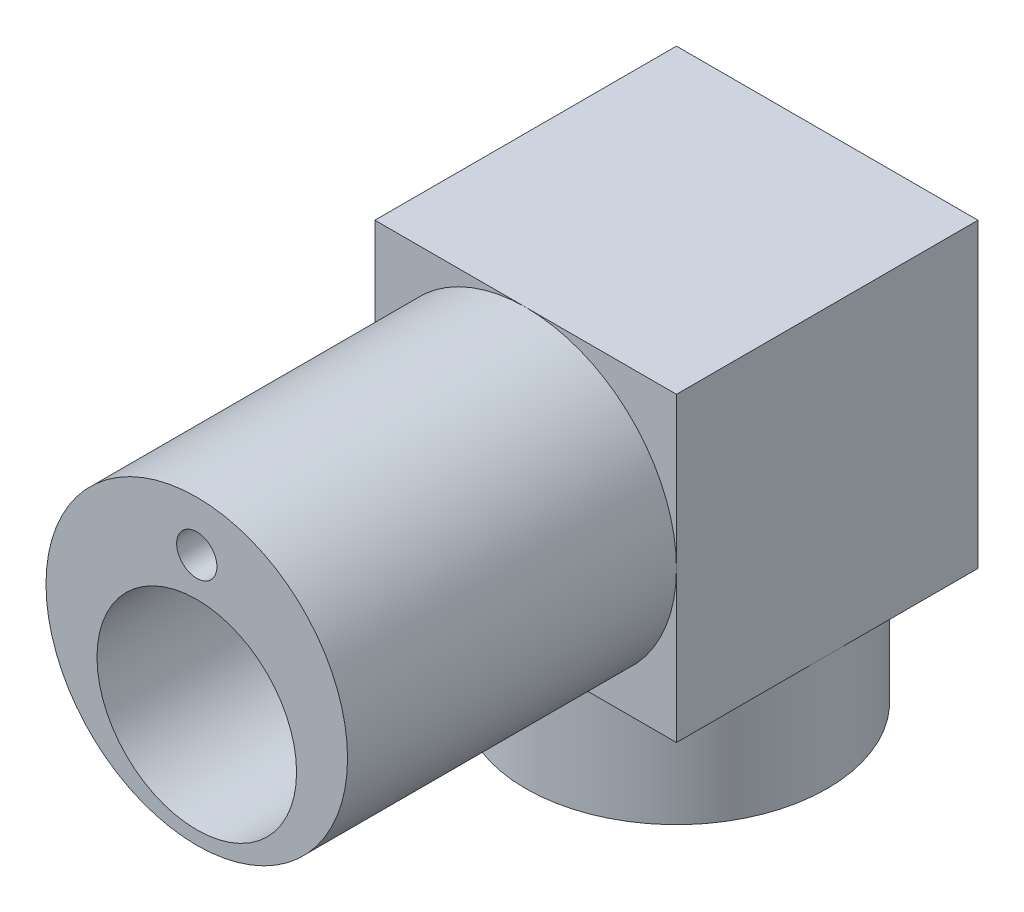
SolidWorks part; units mm, degrees
ref_plane "Front Plane" through (0, 0, 0) normal (0, 0, 1) x (1, 0, 0)
ref_plane "Top Plane" through (0, 0, 0) normal (0, 1, 0) x (1, 0, 0)
ref_plane "Right Plane" through (0, 0, 0) normal (1, 0, 0) x (0, 0, -1)
sketch "Sketch1" plane through (0, 0, 0) normal (0, 0, 1) x (1, 0, 0)
  circle A0 centre (0, 0) radius 28.1
extrude "Boss-Extrude2" add sketch "Sketch1" along normal blind 61.3
sketch "Sketch3" plane through (0, 0, 61.3) normal (0, 0, 1) x (1, 0, 0)
  circle A1 centre (0, -7) radius 18.6
extrude "Cut-Extrude2" cut sketch "Sketch3" against normal blind 58.8 contours A1
sketch "Sketch4" plane through (0, 0, 0) normal (0, 0, -1) x (-1, 0, 0)
  line L1 (-28.1, -28.1) -> (28.1, -28.1)
  line L2 (-28.1, -28.1) -> (-28.1, 28.1)
  line L3 (-28.1, 28.1) -> (28.1, 28.1)
  line L4 (28.1, -28.1) -> (28.1, 28.1)
  line L5 (-28.1, -28.1) -> (28.1, 28.1) construction
  line L6 (-28.1, 28.1) -> (28.1, -28.1) construction
  point P0 (0, 0)
extrude "Boss-Extrude3" add sketch "Sketch4" along normal blind 56.2
sketch "Sketch5" plane through (0, 0, 2.5) normal (0, 0, 1) x (1, 0, 0)
  circle A1 centre (0, -7) radius 16.1
extrude "Cut-Extrude4" cut sketch "Sketch5" against normal blind 5
sketch "Sketch6" plane through (0, 0, -56.2) normal (0, 0, -1) x (-1, 0, 0)
  line L1 (-24.8987, -24.8896) -> (24.8987, -24.8896)
  line L2 (-24.8987, -24.8896) -> (-24.8987, 24.8896)
  line L3 (-24.8987, 24.8896) -> (24.8987, 24.8896)
  line L4 (24.8987, -24.8896) -> (24.8987, 24.8896)
  line L5 (-24.8987, -24.8896) -> (24.8987, 24.8896) construction
  line L6 (-24.8987, 24.8896) -> (24.8987, -24.8896) construction
  point P0 (0, 0)
extrude "Cut-Extrude5" cut sketch "Sketch6" against normal blind 53.7
sketch "Sketch7" plane through (0, -28.1, 0) normal (0, -1, 0) x (-1, 0, 0)
  circle A0 centre (0, 28.1) radius 28.1
extrude "Boss-Extrude4" add sketch "Sketch7" along normal blind 21.5 contours A0
sketch "Sketch8" plane through (0, -49.6, 0) normal (0, -1, 0) x (-1, 0, 0)
  line L2 (1.6583, 25.8321) -> (-1.6583, 25.8321)
  arc A0 (1.6583, 25.8321) -> (-1.6583, 25.8321) centre (0, 28.3321) ccw
extrude "Cut-Extrude6" cut sketch "Sketch8" against normal blind 21.5
sketch "Sketch9" plane through (0, -49.6, 0) normal (0, -1, 0) x (-1, 0, 0)
  circle A1 centre (0, 28.3321) radius 3
extrude "Cut-Extrude7" cut sketch "Sketch9" against normal blind 9.5
sketch "Sketch10" plane through (0, -49.6, 0) normal (0, -1, 0) x (-1, 0, 0)
  circle A1 centre (0, 28.3321) radius 6.025
extrude "Cut-Extrude8" cut sketch "Sketch10" against normal blind 6.2
sketch "Sketch15" plane through (0, -49.6, 0) normal (0, -1, 0) x (-1, 0, 0)
  line L0 (6.025, 28.3321) -> (-6.025, 28.3321)
  circle A0 centre (0, 28.3321) radius 6.025 construction
  arc A1 (15, 28.3321) -> (-15, 28.3321) centre (0, 28.3321) ccw
sketch3d "3DSketch2"
  line L1 (-15, -49.6, -28.3321) -> (-22.5, -49.6, -28.3321)
  line L2 (-15, -49.6, -28.3321) -> (-15, -20, -28.3321)
  line L3 (-15, -20, -28.3321) -> (-22.5, -20, -28.3321)
  line L4 (-22.5, -49.6, -28.3321) -> (-22.5, -20, -28.3321)
sweep "Cut-Sweep4" cut profiles "3DSketch2" path "Sketch15"
sketch "Sketch18" plane through (0, 0, 61.3) normal (0, 0, 1) x (1, 0, 0)
  circle A1 centre (0, 18.75) radius 3.75
extrude "Cut-Extrude9" cut sketch "Sketch18" against normal blind 100
sketch "Sketch19" plane through (0, -49.6, 0) normal (0, -1, 0) x (-1, 0, 0)
  circle A0 centre (-18.75, 28.3321) radius 3.75
  circle A1 centre (18.75, 28.3321) radius 3.75
extrude "Cut-Extrude11" cut sketch "Sketch19" against normal blind 25
